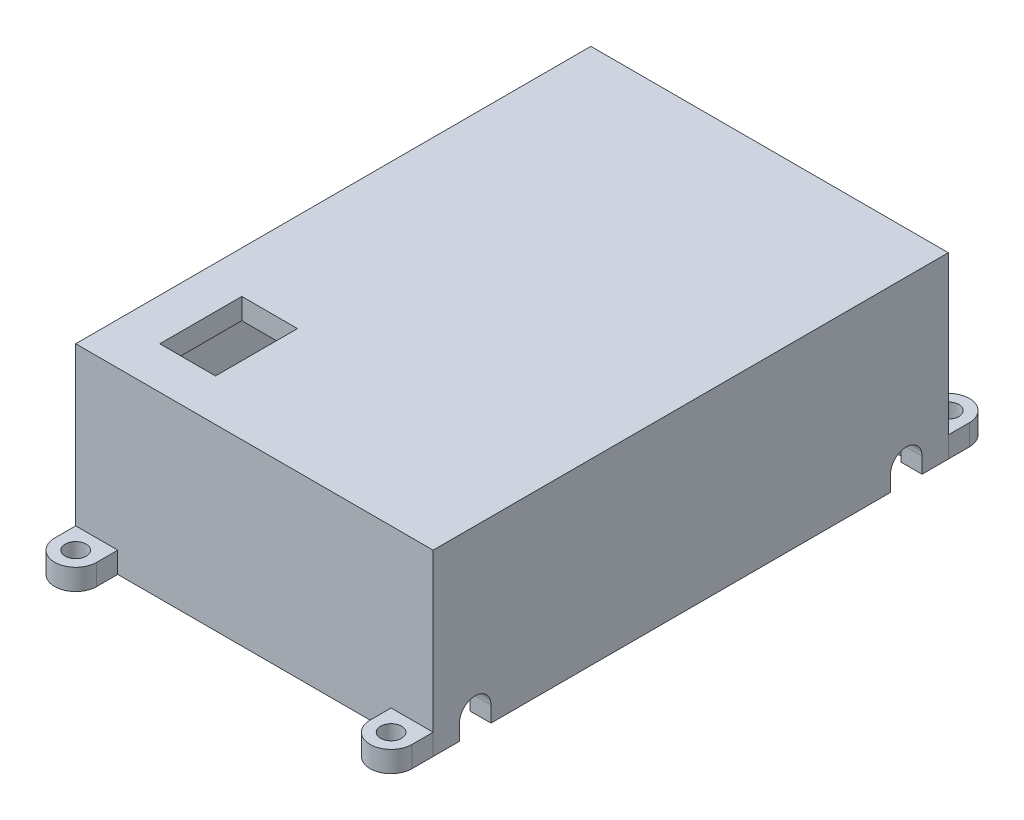
SolidWorks part; units mm, degrees
ref_plane "Front Plane" through (0, 0, 0) normal (0, 0, 1) x (1, 0, 0)
ref_plane "Top Plane" through (0, 0, 0) normal (0, 1, 0) x (1, 0, 0)
ref_plane "Right Plane" through (0, 0, 0) normal (1, 0, 0) x (0, 0, -1)
sketch "Sketch1" plane through (0, 0, 0) normal (0, 1, 0) x (1, 0, 0)
  line L1 (-38.1, -57.15) -> (38.1, -57.15)
  line L2 (-38.1, -57.15) -> (-38.1, 57.15)
  line L3 (-38.1, 57.15) -> (38.1, 57.15)
  line L4 (38.1, -57.15) -> (38.1, 57.15)
  line L5 (-38.1, -57.15) -> (38.1, 57.15) construction
  line L6 (-38.1, 57.15) -> (38.1, -57.15) construction
  point P0 (0, 0)
  dimension "D1" = 114.3
  dimension "D2" = 76.2
extrude "Boss-Extrude1" add sketch "Sketch1" along normal blind 38.1
shell "Shell1" thickness 5.08
sketch "Sketch2" plane through (0, 0, 0) normal (0, -1, 0) x (1, 0, 0)
  line L0 (0, 0) -> (8.6538, 0)
  line L1 (-33.02, 72.39) -> (-43.18, 72.39)
  line L2 (-33.02, 72.39) -> (-33.02, 62.23)
  line L3 (-33.02, 62.23) -> (-43.18, 62.23)
  line L4 (-43.18, 72.39) -> (-43.18, 62.23)
  line L5 (-33.02, 72.39) -> (-43.18, 62.23) construction
  line L6 (-33.02, 62.23) -> (-43.18, 72.39) construction
  line L7 (0, 0) -> (0, 10.2471)
  line L8 (33.02, 62.23) -> (43.18, 72.39) construction
  line L9 (33.02, 72.39) -> (43.18, 62.23) construction
  line L10 (43.18, 72.39) -> (43.18, 62.23)
  line L11 (33.02, 62.23) -> (43.18, 62.23)
  line L12 (33.02, 72.39) -> (33.02, 62.23)
  line L13 (33.02, 72.39) -> (43.18, 72.39)
  line L14 (33.02, -72.39) -> (43.18, -62.23) construction
  line L15 (33.02, -62.23) -> (43.18, -72.39) construction
  line L16 (-33.02, -62.23) -> (-43.18, -72.39) construction
  line L17 (-33.02, -72.39) -> (-43.18, -62.23) construction
  line L18 (33.02, -72.39) -> (43.18, -72.39)
  line L19 (33.02, -72.39) -> (33.02, -62.23)
  line L20 (33.02, -62.23) -> (43.18, -62.23)
  line L21 (43.18, -72.39) -> (43.18, -62.23)
  line L22 (-43.18, -72.39) -> (-43.18, -62.23)
  line L23 (-33.02, -62.23) -> (-43.18, -62.23)
  line L24 (-33.02, -72.39) -> (-33.02, -62.23)
  line L25 (-33.02, -72.39) -> (-43.18, -72.39)
  circle A0 centre (-38.1, 67.31) radius 5.08
  circle A1 centre (-38.1, 67.31) radius 2.54
  circle A2 centre (38.1, 67.31) radius 2.54
  circle A3 centre (38.1, 67.31) radius 5.08
  circle A4 centre (38.1, -67.31) radius 5.08
  circle A5 centre (38.1, -67.31) radius 2.54
  circle A6 centre (-38.1, -67.31) radius 2.54
  circle A7 centre (-38.1, -67.31) radius 5.08
  point P0 (-38.1, 67.31)
  point P20 (38.1, 67.31)
  point P35 (38.1, -67.31)
  point P36 (-38.1, -67.31)
  line M10 (43.18, 62.23) -> (-43.18, 62.23)
  line M12 (-43.18, -62.23) -> (43.18, -62.23)
  dimension "D3" = 5.08
  dimension "D1" = 10.16
  dimension "D2" = 10.16
extrude "Boss-Extrude2" add sketch "Sketch2" against normal blind 5.08 separate body contours A0 A1 | A0 L2 M10 | A0 L4 L3 | A3 A2 | L11 A3 L12 | L10 A3 M10 | A4 A5 | A4 L19 M12 | A4 L21 L20 | A7 A6 | L23 A7 L24 | L22 A7 M12
sketch "Sketch3" plane through (43.18, 0, 0) normal (1, 0, 0) x (0, 0, -1)
  line L0 (-52.07, -3.81) -> (-52.07, 3.81) construction
  line L1 (-62.23, 0) -> (62.23, 0) construction
  line L2 (-55.88, -3.81) -> (-55.88, 3.81)
  line L3 (-48.26, -3.81) -> (-48.26, 3.81)
  line L4 (-62.23, 43.18) -> (-62.23, 0) construction
  line L5 (0, 0) -> (0, 7.7567)
  line L6 (52.07, -3.81) -> (52.07, 3.81) construction
  line L7 (55.88, -3.81) -> (55.88, 3.81)
  line L8 (48.26, -3.81) -> (48.26, 3.81)
  arc A0 (-55.88, -3.81) -> (-48.26, -3.81) centre (-52.07, -3.81) ccw
  arc A1 (-48.26, 3.81) -> (-55.88, 3.81) centre (-52.07, 3.81) ccw
  arc A2 (55.88, -3.81) -> (48.26, -3.81) centre (52.07, -3.81) cw
  arc A3 (48.26, 3.81) -> (55.88, 3.81) centre (52.07, 3.81) cw
  point P4 (-52.07, 0)
  point P16 (52.07, 0)
  line M6 (-62.23, 0) -> (62.23, 0)
  dimension "D2" = 3.81
  dimension "D1" = 10.16
  dimension "D3" = 3.81
extrude "Cut-Extrude1" cut sketch "Sketch3" against normal through all contours L3 A1 L2 M6 | A3 L8 L7 M6
sketch "Sketch4" plane through (0, 43.18, 0) normal (0, 1, 0) x (1, 0, 0)
  line L0 (-43.18, -62.23) -> (43.18, -62.23) construction
  line L1 (-33.02, -32.258) -> (-19.558, -32.258)
  line L2 (-33.02, -32.258) -> (-33.02, -52.07)
  line L3 (-33.02, -52.07) -> (-19.558, -52.07)
  line L4 (-19.558, -32.258) -> (-19.558, -52.07)
  line L5 (-43.18, 62.23) -> (-43.18, -62.23) construction
  dimension "D1" = 19.812
  dimension "D2" = 13.462
  dimension "D3" = 10.16
  dimension "D4" = 10.16
extrude "Cut-Extrude2" cut sketch "Sketch4" against normal through all
